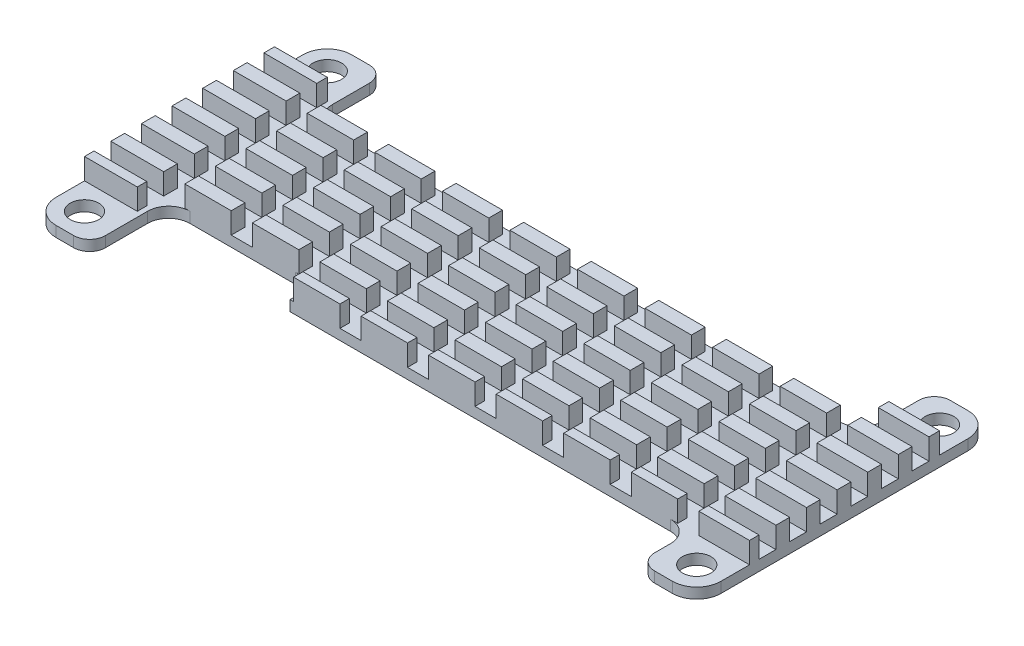
SolidWorks part; units mm, degrees
ref_plane "前视基准面" through (0, 0, 0) normal (0, 0, 1) x (1, 0, 0)
ref_plane "上视基准面" through (0, 0, 0) normal (0, 1, 0) x (1, 0, 0)
ref_plane "右视基准面" through (0, 0, 0) normal (1, 0, 0) x (0, 0, -1)
sketch "草图1" plane through (0, 0, 0) normal (0, 1, 0) x (1, 0, 0)
  line L0 (26.02, 14) -> (31.5, 14)
  line L1 (-31.5, 14) -> (-26.02, 14)
  line L2 (-31.5, 14) -> (-31.5, -14)
  line L3 (-31.5, -14) -> (-26.02, -14)
  line L4 (31.5, 14) -> (31.5, -14)
  line L5 (-31.5, 14) -> (31.5, -14) construction
  line L6 (-31.5, -14) -> (31.5, 14) construction
  line L7 (-29, 11.5) -> (29, 11.5) construction
  line L8 (-29, 11.5) -> (-29, -11.5) construction
  line L9 (-29, -11.5) -> (29, -11.5) construction
  line L10 (29, 11.5) -> (29, -11.5) construction
  line L11 (-29, 11.5) -> (29, -11.5) construction
  line L12 (-29, -11.5) -> (29, 11.5) construction
  line L14 (-26.02, 14) -> (-26.02, 7)
  line L15 (-26.02, 7) -> (26.02, 7)
  line L16 (26.02, 14) -> (26.02, 7)
  line L18 (-26.02, -14) -> (-26.02, -9)
  line L19 (-26.02, -9) -> (26.02, -9)
  line L20 (26.02, -14) -> (26.02, -9)
  line L21 (26.02, -14) -> (31.5, -14)
  circle A0 centre (-29, 11.5) radius 1.35
  circle A1 centre (29, 11.5) radius 1.35
  circle A2 centre (29, -11.5) radius 1.35
  circle A3 centre (-29, -11.5) radius 1.35
  point P0 (0, 0)
  point P6 (0, 0)
  dimension "D5" = 2.7
  dimension "D6" = 2.7
  dimension "D7" = 2.7
  dimension "D8" = 2.7
  dimension "D1" = 28
  dimension "D2" = 63
  dimension "D3" = 23
  dimension "D4" = 58
  dimension "D9" = 5.48
  dimension "D10" = 5.48
  dimension "D11" = 5.48
  dimension "D12" = 5.48
  dimension "D13" = 7
  dimension "D14" = 5
extrude "凸台-拉伸1" add sketch "草图1" along normal blind 3
fillet "圆角1" radius 2.3 4 edges at (31.5, 1.5, 14) (31.5, 1.5, -14) (-31.5, 1.5, -14) (-31.5, 1.5, 14)
fillet "圆角2" radius 1.5 4 edges at (-26.02, 1.5, 14) (-26.02, 1.5, -14) (26.02, 1.5, -14) (26.02, 1.5, 14)
sketch "草图2" plane through (0, 3, 0) normal (0, 1, 0) x (1, 0, 0)
  line L1 (-12.02, -6.5) -> (-26.02, -6.5)
  line L2 (-12.02, -6.5) -> (-12.02, -9)
  line L3 (-12.02, -9) -> (-26.02, -9)
  line L4 (-26.02, -6.5) -> (-26.02, -9)
  dimension "D1" = 14
  dimension "D2" = 2.5
extrude "切除-拉伸1" cut sketch "草图2" against normal blind 10
sketch "草图3" plane through (0, 3, 0) normal (0, 1, 0) x (1, 0, 0)
  line L0 (-12.02, -9) -> (26.02, -9) construction
  line L1 (-35.0428, 17.5975) -> (37.51, 17.5975)
  line L2 (-35.0428, 17.5975) -> (-35.0428, 9)
  line L3 (-35.0428, 9) -> (37.51, 9)
  line L4 (37.51, 17.5975) -> (37.51, 9)
  line L5 (-39.2412, -9) -> (37.51, -9)
  line L6 (-39.2412, -9) -> (-39.2412, -18.7462)
  line L7 (-39.2412, -18.7462) -> (37.51, -18.7462)
  line L8 (37.51, -9) -> (37.51, -18.7462)
  line L9 (26.02, 7) -> (-26.02, 7) construction
  dimension "D1" = 0
  dimension "D2" = 2
extrude "切除-拉伸2" cut sketch "草图3" against normal blind 2
fillet "圆角3" radius 2 5 edges at (-12.02, 1.5, 6.5) (-26.02, 1.5, 6.5) (26.02, 0.5, 9) (-26.02, 1.5, -7) (26.02, 1.5, -7)
sketch "草图4" plane through (0, 3, 0) normal (0, 1, 0) x (1, 0, 0)
  line L0 (31.5, -9) -> (31.5, 9) construction
  line L5 (-31.5, 8) -> (31.5, 8)
  line L6 (-31.5, 8) -> (-31.5, 6.4)
  line L7 (-31.5, 6.4) -> (31.5, 6.4)
  line L8 (31.5, 8) -> (31.5, 6.4)
  line L11 (-31.5, 9) -> (-26.02, 9) construction
  line L13 (-31.5, 9) -> (-31.5, -9) construction
  line L14 (-31.5, 5.1) -> (-31.5, 3.5)
  line L15 (-31.5, 5.1) -> (31.5, 5.1)
  line L16 (31.5, 5.1) -> (31.5, 3.5)
  line L17 (-31.5, 3.5) -> (31.5, 3.5)
  line L18 (-31.5, 2.2) -> (-31.5, 0.6)
  line L19 (-31.5, 2.2) -> (31.5, 2.2)
  line L20 (31.5, 2.2) -> (31.5, 0.6)
  line L21 (-31.5, 0.6) -> (31.5, 0.6)
  line L22 (-31.5, -0.7) -> (-31.5, -2.3)
  line L23 (-31.5, -0.7) -> (31.5, -0.7)
  line L24 (31.5, -0.7) -> (31.5, -2.3)
  line L25 (-31.5, -2.3) -> (31.5, -2.3)
  line L26 (-31.5, -3.6) -> (-31.5, -5.2)
  line L27 (-31.5, -3.6) -> (31.5, -3.6)
  line L28 (31.5, -3.6) -> (31.5, -5.2)
  line L29 (-31.5, -5.2) -> (31.5, -5.2)
  line L30 (-31.5, -6.5) -> (-31.5, -8.1)
  line L31 (-31.5, -6.5) -> (31.5, -6.5)
  line L32 (31.5, -6.5) -> (31.5, -8.1)
  line L33 (-31.5, -8.1) -> (31.5, -8.1)
  dimension "D1" = 1.6
  dimension "D2" = 1
  dimension "D3" = 6
extrude "切除-拉伸4" cut sketch "草图4" against normal blind 2
sketch "草图5" plane through (0, 3, 0) normal (0, 1, 0) x (1, 0, 0)
  line L0 (-31.5, 9) -> (-26.02, 9) construction
  line L1 (-26.5, 9) -> (-24.5, 9)
  line L2 (-26.5, 9) -> (-26.5, -9)
  line L3 (-26.5, -9) -> (-24.5, -9)
  line L4 (-24.5, 9) -> (-24.5, -9)
  line L5 (-12.02, -9) -> (31.5, -9) construction
  line L6 (-31.5, 2.2) -> (-31.5, 0.6) construction
  line L7 (-20.1, 9) -> (-18.1, 9)
  line L8 (-20.1, 9) -> (-20.1, -9)
  line L9 (-20.1, -9) -> (-18.1, -9)
  line L10 (-18.1, 9) -> (-18.1, -9)
  line L11 (-13.7, 9) -> (-11.7, 9)
  line L12 (-13.7, 9) -> (-13.7, -9)
  line L13 (-13.7, -9) -> (-11.7, -9)
  line L14 (-11.7, 9) -> (-11.7, -9)
  line L15 (-7.3, 9) -> (-5.3, 9)
  line L16 (-7.3, 9) -> (-7.3, -9)
  line L17 (-7.3, -9) -> (-5.3, -9)
  line L18 (-5.3, 9) -> (-5.3, -9)
  line L19 (-0.9, 9) -> (1.1, 9)
  line L20 (-0.9, 9) -> (-0.9, -9)
  line L21 (-0.9, -9) -> (1.1, -9)
  line L22 (1.1, 9) -> (1.1, -9)
  line L23 (5.5, 9) -> (7.5, 9)
  line L24 (5.5, 9) -> (5.5, -9)
  line L25 (5.5, -9) -> (7.5, -9)
  line L26 (7.5, 9) -> (7.5, -9)
  line L27 (11.9, 9) -> (13.9, 9)
  line L28 (11.9, 9) -> (11.9, -9)
  line L29 (11.9, -9) -> (13.9, -9)
  line L30 (13.9, 9) -> (13.9, -9)
  line L31 (18.3, 9) -> (20.3, 9)
  line L32 (18.3, 9) -> (18.3, -9)
  line L33 (18.3, -9) -> (20.3, -9)
  line L34 (20.3, 9) -> (20.3, -9)
  line L35 (24.7, 9) -> (26.7, 9)
  line L36 (24.7, 9) -> (24.7, -9)
  line L37 (24.7, -9) -> (26.7, -9)
  line L38 (26.7, 9) -> (26.7, -9)
  dimension "D1" = 5
  dimension "D2" = 2
  dimension "D3" = 9
extrude "切除-拉伸5" cut sketch "草图5" against normal blind 2
